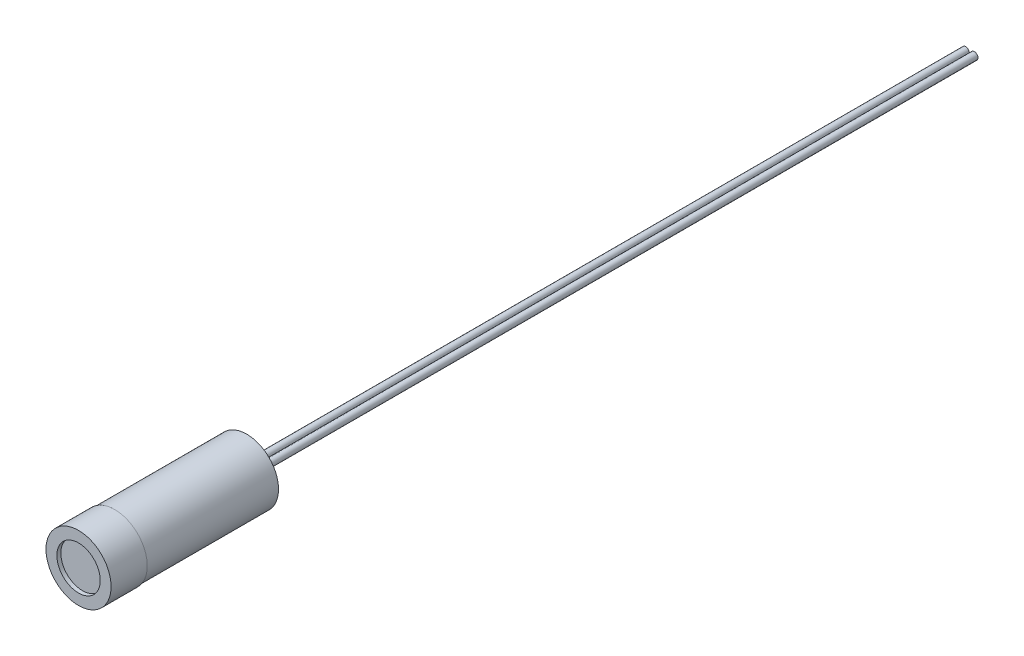
SolidWorks part; units mm, degrees
ref_plane "Front Plane" through (0, 0, 0) normal (0, 0, 1) x (1, 0, 0)
ref_plane "Top Plane" through (0, 0, 0) normal (0, 1, 0) x (1, 0, 0)
ref_plane "Right Plane" through (0, 0, 0) normal (1, 0, 0) x (0, 0, -1)
sketch "Sketch1" plane through (0, 0, 0) normal (1, 0, 0) x (0, 0, -1)
  line L0 (0, 4.5) -> (0, 3)
  line L1 (0, 3) -> (0.55, 3)
  line L2 (0.55, 3) -> (0.55, 0)
  line L3 (0.55, 0) -> (23.25, 0)
  line L4 (23.25, 0) -> (23.25, 4.4)
  line L5 (23.25, 4.4) -> (5, 4.4)
  line L6 (5, 4.4) -> (5, 4.5)
  line L7 (5, 4.5) -> (0, 4.5)
  line L8 (0, 0) -> (-12.7341, 0) construction
  dimension "D1" = 9
  dimension "D2" = 6
  dimension "D3" = 0.55
  dimension "D4" = 5
  dimension "D5" = 8.8
  dimension "D6" = 23.25
revolve "Revolve1" add sketch "Sketch1" angle 360 about L8
sketch "Sketch2" plane through (0, 0, -23.25) normal (0, 0, -1) x (-1, 0, 0)
  line L0 (0, 0) -> (-0.6, 0) construction
  line L1 (0, 0) -> (0, -0.6433) construction
  circle A0 centre (-0.6, 0) radius 0.5
  dimension "D1" = 1
  dimension "D2" = 0.6
extrude "Boss-Extrude1" add sketch "Sketch2" along normal blind 100
mirror "Mirror1" about plane through (0, 0, 0) normal (1, 0, 0) of "Boss-Extrude1"
